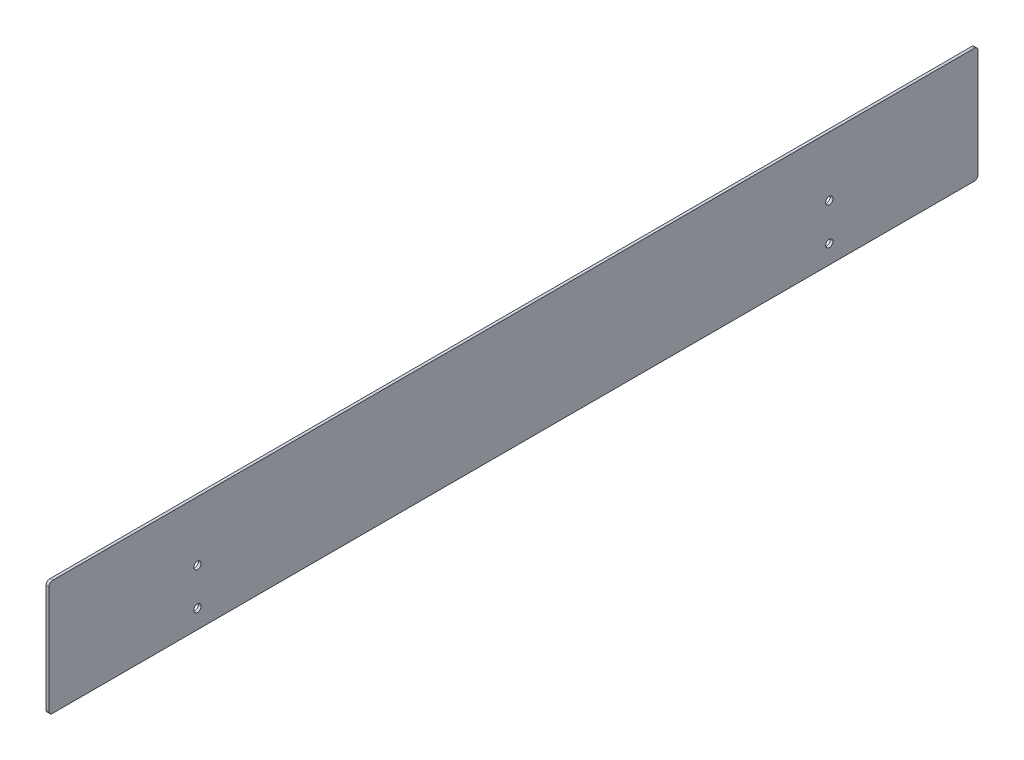
SolidWorks part; units mm, degrees
ref_plane "Front Plane" through (0, 0, 0) normal (0, 0, 1) x (1, 0, 0)
ref_plane "Top Plane" through (0, 0, 0) normal (0, 1, 0) x (1, 0, 0)
ref_plane "Right Plane" through (0, 0, 0) normal (1, 0, 0) x (0, 0, -1)
sketch "Sketch1" plane through (0, 0, 0) normal (1, 0, 0) x (0, 0, -1)
  line L1 (-261.3393, -78.2926) -> (238.6607, -78.2926)
  line L2 (-261.3393, -78.2926) -> (-261.3393, -140.2926)
  line L3 (-261.3393, -140.2926) -> (238.6607, -140.2926)
  line L4 (238.6607, -78.2926) -> (238.6607, -140.2926)
  circle A0 centre (158.6607, -110.2926) radius 1.95
  circle A1 centre (158.6607, -130.2926) radius 1.95
  circle A2 centre (-181.3393, -110.2926) radius 1.95
  circle A3 centre (-181.3393, -130.2926) radius 1.95
  dimension "D3" = 80
  dimension "D1" = 500
  dimension "D2" = 62
  dimension "D4" = 20
  dimension "D5" = 10
  dimension "D6" = 80
  dimension "D7" = 20
  dimension "D8" = 10
extrude "Boss-Extrude1" add sketch "Sketch1" along normal blind 1.5
fillet "Fillet1" radius 2 4 edges at (0.75, -140.2926, -238.6607) (0.75, -78.2926, -238.6607) (0.75, -140.2926, 261.3393) (0.75, -78.2926, 261.3393)
